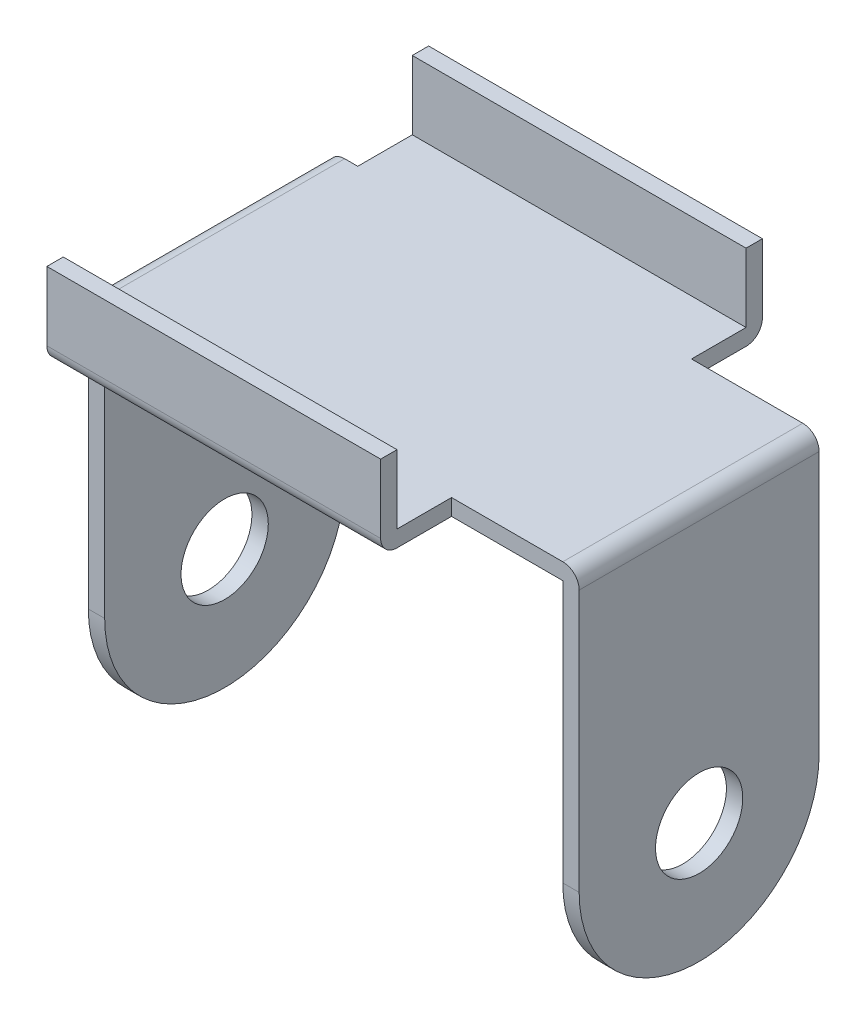
SolidWorks part; units mm, degrees
ref_plane "Front Plane" through (0, 0, 0) normal (0, 0, 1) x (1, 0, 0)
ref_plane "Top Plane" through (0, 0, 0) normal (0, 1, 0) x (1, 0, 0)
ref_plane "Right Plane" through (0, 0, 0) normal (1, 0, 0) x (0, 0, -1)
ref_plane "Plane1" through (-22.5, 0, 0) normal (-1, 0, 0) x (0, -1, 0)
sketch "Sketch1" plane through (-22.5, 0, 0) normal (-1, 0, 0) x (0, -1, 0)
  line L0 (-25.5, -11) -> (0, -11)
  line L1 (0, 11) -> (-25.5, 11)
  line L2 (-25.5, 11) -> (-25.5, -11)
  arc A0 (0, -11) -> (0, 11) centre (0, 0) ccw
extrude "Boss-Extrude1" add sketch "Sketch1" against normal blind 45
sketch "Sketch2" plane through (0, 0, 11) normal (0, 0, 1) x (1, 0, 0)
  line L0 (-21, -17.8827) -> (21, -17.8827)
  line L1 (21, -17.8827) -> (21, 24)
  line L2 (21, 24) -> (-21, 24)
  line L3 (-21, 24) -> (-21, -17.8827)
extrude "Cut-Extrude1" cut sketch "Sketch2" against normal through all
sketch "Sketch3" plane through (0, 0, -11) normal (0, 0, -1) x (-1, 0, 0)
  line L0 (19.8, 25.5) -> (19.8, 24)
  line L1 (19.8, 24) -> (-10.8, 24)
  line L2 (-10.8, 24) -> (-10.8, 25.5)
  line L3 (-10.8, 25.5) -> (19.8, 25.5)
extrude "Boss-Extrude2" add sketch "Sketch3" along normal blind 6.5
sketch "Sketch4" plane through (0, 25.5, 0) normal (0, 1, 0) x (-1, 0, 0)
  line L0 (19.8, -17.5) -> (-10.8, -17.5)
  line L1 (-10.8, -17.5) -> (-10.8, -16)
  line L2 (-10.8, -16) -> (19.8, -16)
  line L3 (19.8, -16) -> (19.8, -17.5)
extrude "Boss-Extrude3" add sketch "Sketch4" along normal blind 6.3
sketch "Sketch5" plane through (0, 0, 11) normal (0, 0, 1) x (1, 0, 0)
  line L0 (10.8, 25.5) -> (10.8, 24)
  line L1 (10.8, 24) -> (-19.8, 24)
  line L2 (-19.8, 24) -> (-19.8, 25.5)
  line L3 (-19.8, 25.5) -> (10.8, 25.5)
extrude "Boss-Extrude4" add sketch "Sketch5" along normal blind 6.5
sketch "Sketch6" plane through (0, 25.5, 0) normal (0, 1, 0) x (-1, 0, 0)
  line L0 (-10.8, 17.5) -> (19.8, 17.5)
  line L1 (19.8, 17.5) -> (19.8, 16)
  line L2 (19.8, 16) -> (-10.8, 16)
  line L3 (-10.8, 16) -> (-10.8, 17.5)
extrude "Boss-Extrude5" add sketch "Sketch6" along normal blind 6.3
hole_wizard "Ø8.0 (8) Diameter Hole1" positions "Sketch8" profile "Sketch7" hole size "Ø8.0" standard "ANSI Metric"
sketch "Sketch8" plane through (21, 0, 0) normal (-1, 0, 0) x (0, 0, 1)
  point P0 (0, 0)
sketch "Sketch7" plane through (21, 0, 0) normal (0, 1, 0) x (0, 0, 1)
  line L0 (0, 0) -> (0, 1.5)
  line L1 (0, 1.5) -> (4, 1.5)
  line L2 (4, 1.5) -> (4, 0)
  line L5 (4, 0) -> (0, 0)
  line L11 (0, -6.35) -> (0, 107.95) construction
  dimension "Thru Hole Dia." = 8
  dimension "Thru Hole Depth" = 1.5
hole_wizard "Ø8.0 (8) Diameter Hole2" positions "Sketch10" profile "Sketch9" hole size "Ø8.0" standard "ANSI Metric"
sketch "Sketch10" plane through (-21, 0, 0) normal (1, 0, 0) x (0, 0, -1)
  point P0 (0, 0)
sketch "Sketch9" plane through (-21, 0, 0) normal (0, 1, 0) x (0, 0, -1)
  line L0 (0, 0) -> (0, 1.5)
  line L1 (0, 1.5) -> (4, 1.5)
  line L2 (4, 1.5) -> (4, 0)
  line L5 (4, 0) -> (0, 0)
  line L11 (0, -6.35) -> (0, 107.95) construction
  dimension "Thru Hole Dia." = 8
  dimension "Thru Hole Depth" = 1.5
fillet "Fillet1" radius 1.5 4 edges at (-4.5, 24, 17.5) (-4.5, 24, -17.5) (-22.5, 25.5, 0) (22.5, 25.5, 0)
